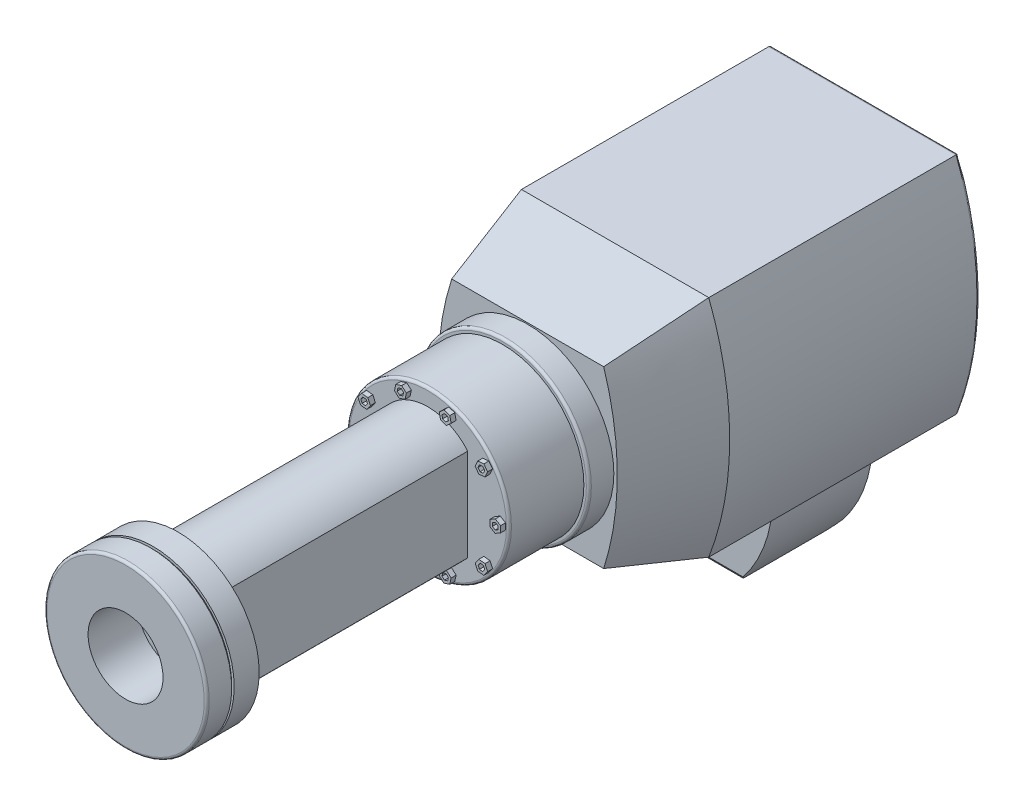
SolidWorks part; units mm, degrees
ref_plane "Front Plane" through (0, 0, 0) normal (0, 0, 1) x (1, 0, 0)
ref_plane "Top Plane" through (0, 0, 0) normal (0, 1, 0) x (1, 0, 0)
ref_plane "Right Plane" through (0, 0, 0) normal (1, 0, 0) x (0, 0, -1)
sketch "Sketch1" plane through (0, 0, 0) normal (0, 0, 1) x (1, 0, 0)
  line L0 (0, 45) -> (0, -45) construction
  line L1 (-37.5, 45) -> (37.5, 45)
  line L2 (-37.5, -45) -> (37.5, -45)
  arc A0 (-37.5, 45) -> (-37.5, -45) centre (79.119, 0) ccw
  arc A1 (37.5, 45) -> (37.5, -45) centre (-79.119, 0) cw
  point P4 (0, 0)
  point P8 (0, 45)
  point P11 (0, -45)
  dimension "D3" = 125
  dimension "D1" = 90
  dimension "D2" = 75
extrude "Boss-Extrude1" add sketch "Sketch1" along normal blind 100
sketch "Sketch4" plane through (0, 0, 100) normal (0, 0, 1) x (1, 0, 0)
  line L2 (37.5, 45) -> (-37.5, 45)
  line L3 (-37.5, -45) -> (37.5, -45)
  line L4 (37.5, 45) -> (-37.5, 45)
  line L5 (-37.5, -45) -> (37.5, -45)
  arc A2 (37.5, -45) -> (37.5, 45) centre (-79.119, 0) ccw
  arc A3 (-37.5, 45) -> (-37.5, -45) centre (79.119, 0) ccw
  arc A4 (37.5, -45) -> (37.5, 45) centre (-79.119, 0) ccw
  arc A5 (-37.5, 45) -> (-37.5, -45) centre (79.119, 0) ccw
  dimension "D1" = 0
ref_plane "Plane2" through (0, 0, 135) normal (0, 0, 1) x (1, 0, 0)
sketch "Sketch6" plane through (0, 0, 135) normal (0, 0, 1) x (1, 0, 0)
  line L4 (30.4255, 35) -> (-30.4255, 35)
  line L5 (-30.4255, -35) -> (30.4255, -35)
  line L6 (30.4255, 35) -> (-30.4255, 35)
  line L7 (-30.4255, -35) -> (30.4255, -35)
  arc A4 (30.4255, -35) -> (30.4255, 35) centre (-79.119, 0) ccw
  arc A5 (-30.4255, 35) -> (-30.4255, -35) centre (79.119, 0) ccw
  arc A6 (30.4255, -35) -> (30.4255, 35) centre (-79.119, 0) ccw
  arc A7 (-30.4255, 35) -> (-30.4255, -35) centre (79.119, 0) ccw
  dimension "D1" = 10
loft "Loft2" add profiles "Sketch4", "Sketch6"
sketch "Sketch7" plane through (0, 0, 135) normal (0, 0, 1) x (1, 0, 0)
  circle A0 centre (0, 0) radius 34.5
  dimension "D1" = 69
extrude "Boss-Extrude2" add sketch "Sketch7" along normal blind 10
sketch "Sketch8" plane through (0, 0, 145) normal (0, 0, 1) x (1, 0, 0)
  circle A2 centre (0, 0) radius 32.5
  circle A3 centre (0, 0) radius 32.5
  dimension "D1" = 2
extrude "Boss-Extrude3" add sketch "Sketch8" along normal blind 30
sketch "Sketch9" plane through (0, 0, 175) normal (0, 0, 1) x (1, 0, 0)
  line L0 (0, 0) -> (29, 0) construction
  line L1 (30.1651, 0.6726) -> (29, 1.3453)
  line L2 (29, 2.5) -> (26.8349, 1.25)
  line L3 (26.8349, 1.25) -> (26.8349, -1.25)
  line L4 (26.8349, -1.25) -> (29, -2.5)
  line L5 (29, -2.5) -> (31.1651, -1.25)
  line L6 (31.1651, -1.25) -> (31.1651, 1.25)
  line L7 (31.1651, 1.25) -> (29, 2.5)
  line L8 (29, 1.3453) -> (27.8349, 0.6726)
  line L9 (27.8349, 0.6726) -> (27.8349, -0.6726)
  line L10 (27.8349, -0.6726) -> (29, -1.3453)
  line L11 (29, -1.3453) -> (30.1651, -0.6726)
  line L12 (30.1651, -0.6726) -> (30.1651, 0.6726)
  circle A0 centre (29, 0) radius 2.1651 construction
  dimension "D1" = 29
  dimension "D2" = 5
  dimension "D3" = 1
extrude "Boss-Extrude4" add sketch "Sketch9" along normal blind 2
pattern_circular "CirPattern1" count 10 over 360 about axis through (0, 0, 0) along (0, 0, 1) of "Boss-Extrude4"
sketch "Sketch10" plane through (0, 0, 175) normal (0, 0, 1) x (1, 0, 0)
  line L0 (0, 0) -> (16, 0) construction
  line L1 (0, 16.2537) -> (0, -13.869) construction
  line L2 (16, 18.5) -> (16, -18.5)
  line L3 (-16, 18.5) -> (-16, -18.5)
  arc A0 (-16, 18.5) -> (16, 18.5) centre (0, 4.8985) cw
  arc A1 (-16, -18.5) -> (16, -18.5) centre (0, -4.8985) ccw
  point P8 (16, 0)
  dimension "D3" = 21
  dimension "D1" = 16
  dimension "D2" = 37
extrude "Boss-Extrude5" add sketch "Sketch10" along normal blind 100
sketch "Sketch12" plane through (0, 0, 275) normal (0, 0, 1) x (1, 0, 0)
  circle A0 centre (0, 0) radius 32.5 construction
  circle A1 centre (0, 0) radius 32.5
extrude "Boss-Extrude6" add sketch "Sketch12" along normal blind 10
sketch "Sketch13" plane through (0, 0, 285) normal (0, 0, 1) x (1, 0, 0)
  circle A2 centre (0, 0) radius 31.5
  circle A3 centre (0, 0) radius 31.5
  dimension "D1" = 1
extrude "Boss-Extrude7" add sketch "Sketch13" along normal blind 1
sketch "Sketch14" plane through (0, 0, 286) normal (0, 0, 1) x (1, 0, 0)
  circle A0 centre (0, 0) radius 32.5 construction
  circle A1 centre (0, 0) radius 32.5
extrude "Boss-Extrude8" add sketch "Sketch14" along normal blind 10
ref_plane "Plane3" through (-37.5, 0, 0) normal (1, 0, 0) x (0, 0, -1)
sketch "Sketch15" plane through (-37.5, 0, 0) normal (1, 0, 0) x (0, 0, -1)
  line L0 (-100, -45) -> (0, -45) construction
  circle A0 centre (-50, -45) radius 42.5
  dimension "D1" = 85
extrude "Boss-Extrude9" add sketch "Sketch15" along normal mid plane 21
sketch "Sketch16" plane through (-27, 0, 0) normal (1, 0, 0) x (0, 0, -1)
  line L0 (-50, -45) -> (-50, -75) construction
  line L1 (-92.5, -45) -> (-7.5, -45) construction
  line L2 (-70, -45) -> (-70, -75)
  line L3 (-30, -45) -> (-30, -75)
  line L4 (-70, -45) -> (-30, -45)
  arc A0 (-70, -75) -> (-30, -75) centre (-50, -60.3189) ccw
  dimension "D4" = 24.81
  dimension "D1" = 30
  dimension "D2" = 20
  dimension "D3" = 20
extrude "Boss-Extrude10" add sketch "Sketch16" along normal blind 35
ref_plane "Plane4" through (0, 0, 50) normal (0, 0, 1) x (1, 0, 0)
sketch "Sketch17" plane through (0, 0, 50) normal (0, 0, 1) x (1, 0, 0)
  line L0 (8, -45) -> (8, -87)
  line L1 (8, -45) -> (33, -45)
  line L2 (-37.5, -45) -> (37.5, -45) construction
  arc A0 (8, -87) -> (33, -45) centre (-21.8393, -40.7981) ccw
  dimension "D3" = 55
  dimension "D1" = 25
  dimension "D2" = 42
extrude "Boss-Extrude11" add sketch "Sketch17" along normal mid plane 40
sketch "Sketch18" plane through (8, 0, 0) normal (-1, 0, 0) x (0, 0, 1)
  line L6 (70, -87) -> (70, -75)
  line L7 (30, -75) -> (30, -87)
  line L8 (30, -87) -> (70, -87)
  line L9 (70, -87) -> (70, -75)
  line L10 (30, -75) -> (30, -87)
  line L11 (30, -87) -> (70, -87)
  arc A2 (30, -75) -> (70, -75) centre (50, -60.3189) ccw
  arc A3 (30, -75) -> (70, -75) centre (50, -60.3189) ccw
  dimension "D1" = 0
extrude "Cut-Extrude1" cut sketch "Sketch18" against normal through all
fillet "Fillet1" radius 1 9 edges at (0, 45, 0) (-45.881, 0, 0) (0, -45, 0) (45.881, 0, 0) (32.5, 0, 296) (32.5, 0, 175) (34.5, 0, 145) (-48, -45, 7.5) (-27, -87.5, 50)
sketch "Sketch19" plane through (0, 0, 296) normal (0, 0, 1) x (1, 0, 0)
  circle A0 centre (0, 0) radius 15
  dimension "D1" = 30
extrude "Cut-Extrude2" cut sketch "Sketch19" against normal blind 20
sketch "Sketch20" plane through (-48, 0, 0) normal (-1, 0, 0) x (0, 0, 1)
  circle A0 centre (50, -45) radius 15
  dimension "D1" = 30
extrude "Cut-Extrude3" cut sketch "Sketch20" against normal blind 20
